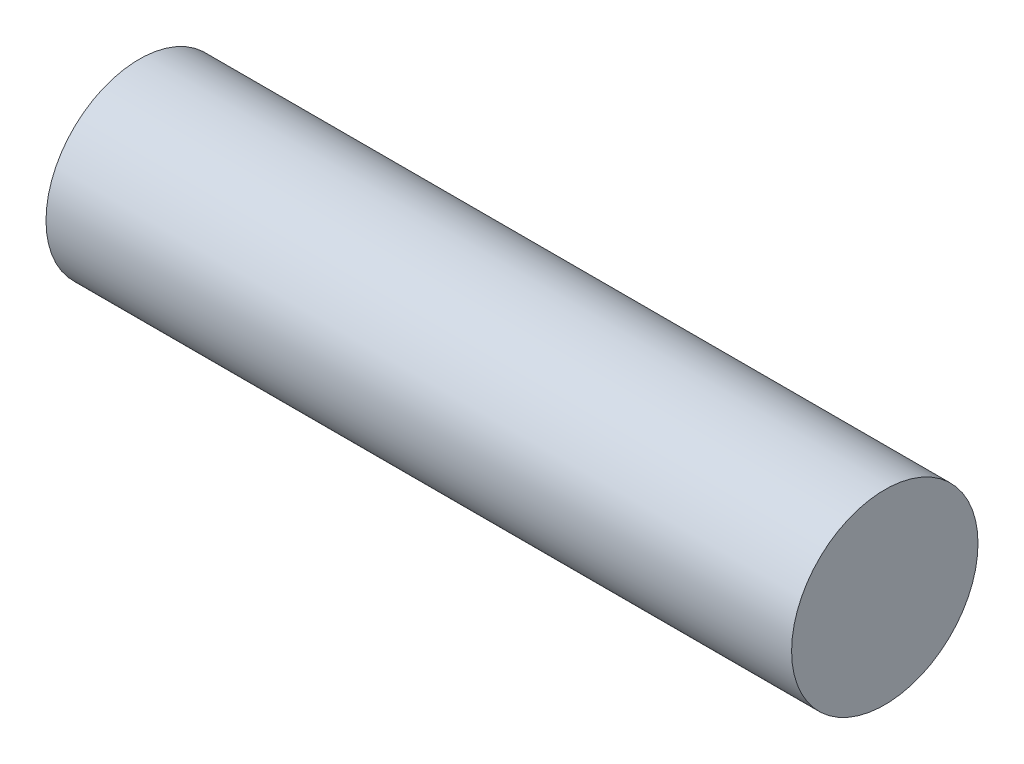
SolidWorks part; units mm, degrees
ref_plane "Front Plane" through (0, 0, 0) normal (0, 0, 1) x (1, 0, 0)
ref_plane "Top Plane" through (0, 0, 0) normal (0, 1, 0) x (1, 0, 0)
ref_plane "Right Plane" through (0, 0, 0) normal (1, 0, 0) x (0, 0, -1)
sketch "Sketch1" plane through (0, 0, 0) normal (1, 0, 0) x (0, 0, -1)
  circle A0 centre (0, 0) radius 5
  dimension "D1" = 10
extrude "Boss-Extrude1" add sketch "Sketch1" along normal blind 40
